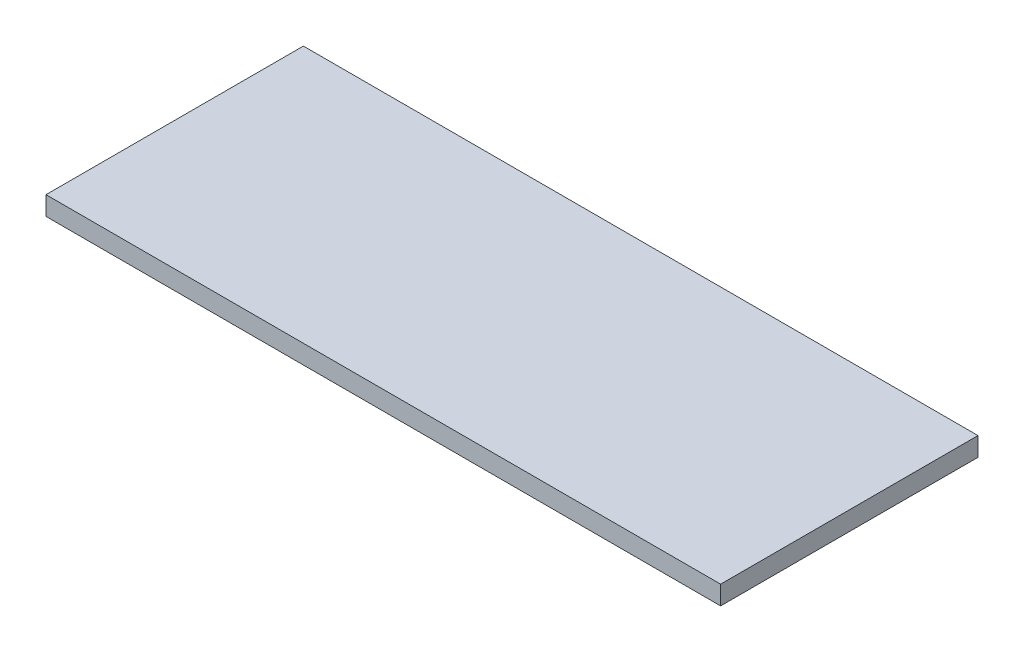
SolidWorks part; units mm, degrees
ref_plane "Спереди" through (0, 0, 0) normal (0, 0, 1) x (1, 0, 0)
ref_plane "Сверху" through (0, 0, 0) normal (0, 1, 0) x (1, 0, 0)
ref_plane "Справа" through (0, 0, 0) normal (1, 0, 0) x (0, 0, -1)
other "Configuration Table"
sketch "Эскиз1" plane through (0, 0, 0) normal (0, 1, 0) x (1, 0, 0)
  line L1 (0, 0) -> (107.3011, 0)
  line L2 (0, 0) -> (0, 40.9382)
  line L3 (0, 40.9382) -> (107.3011, 40.9382)
  line L4 (107.3011, 0) -> (107.3011, 40.9382)
extrude "Основа" add sketch "Эскиз1" along normal blind 3
